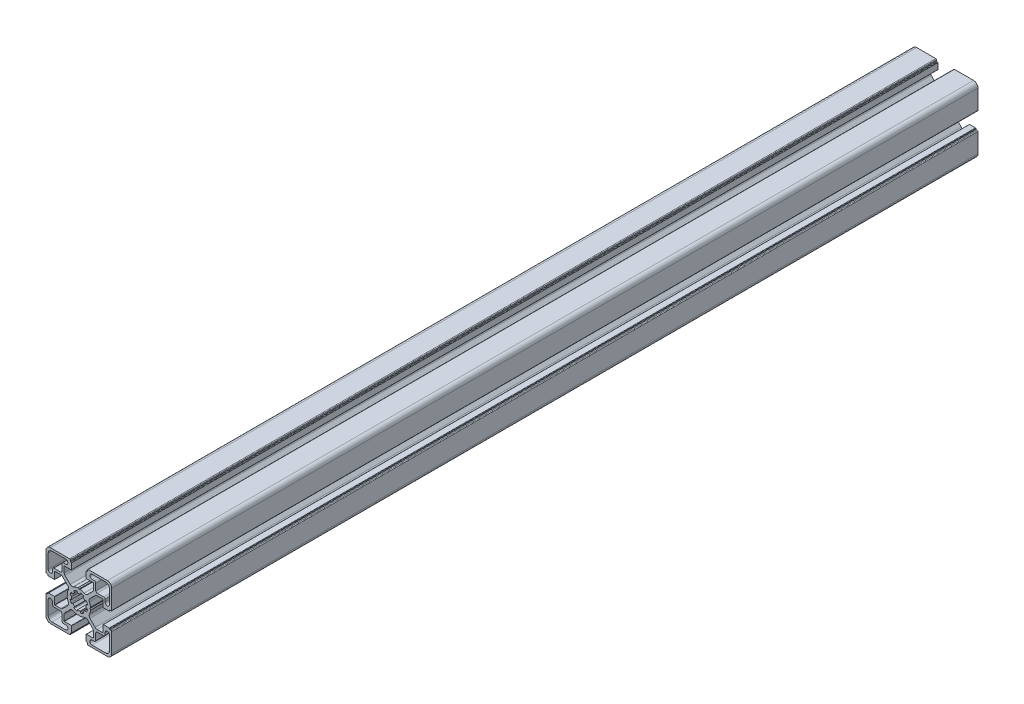
SolidWorks part; units mm, degrees
ref_plane "Front Plane" through (0, 0, 0) normal (0, 0, 1) x (1, 0, 0)
ref_plane "Top Plane" through (0, 0, 0) normal (0, 1, 0) x (1, 0, 0)
ref_plane "Right Plane" through (0, 0, 0) normal (1, 0, 0) x (0, 0, -1)
sketch "Sketch1" plane through (0, 0, 0) normal (0, 0, 1) x (1, 0, 0)
  line L0 (10.55, 18) -> (9, 18)
  line L1 (18.5, 21) -> (9, 21)
  line L2 (21, 9.0002) -> (21, 18.5)
  line L3 (18, 9.0002) -> (18, 10.55)
  line L4 (17, 11.55) -> (12.55, 11.55)
  line L5 (11.55, 12.55) -> (11.55, 17)
  line L6 (7.974, 0.7926) -> (7.5401, 0.0468)
  line L7 (-0.8674, 4.9242) -> (-0.9675, 5.4811)
  line L8 (-3.1913, 4.5626) -> (-2.864, 4.0985)
  line L9 (-4.0897, 2.8765) -> (-4.5668, 3.2082)
  line L10 (-5.4897, 0.9862) -> (-4.9205, 0.8878)
  line L11 (11.1298, 9.425) -> (7.5635, 5.8587)
  line L12 (16.3169, 9.9945) -> (12.5048, 9.9945)
  line L13 (16.5169, 5.2) -> (16.5169, 9.7945)
  line L14 (20.7196, 5) -> (16.7169, 5)
  line L15 (21.0196, 5.3) -> (21.0196, 5.5)
  line L16 (22, 5.8) -> (21.3196, 5.8)
  line L17 (22.5, 6.3) -> (22.5, 19.5)
  line L18 (19.5, 22.5) -> (6.3757, 22.5)
  line L19 (5.8757, 21.3) -> (5.8757, 22)
  line L20 (5.5757, 21) -> (5.3, 21)
  line L21 (5, 16.6668) -> (5, 20.7)
  line L22 (9.9054, 16.4668) -> (5.2, 16.4668)
  line L23 (10.1054, 12.4716) -> (10.1054, 16.2668)
  line L24 (5.9449, 7.4827) -> (9.5196, 11.0574)
  line L25 (0.1126, 7.6069) -> (0.7547, 7.9748)
  line L26 (5.4897, 0.9862) -> (4.9205, 0.8878)
  line L27 (4.0897, 2.8765) -> (4.5668, 3.2082)
  line L28 (3.1913, 4.5626) -> (2.864, 4.0985)
  line L29 (0.8674, 4.9242) -> (0.9675, 5.4811)
  line L30 (-10.55, -18) -> (-9, -18)
  line L31 (-18.5, -21) -> (-9, -21)
  line L32 (-21, -9.0002) -> (-21, -18.5)
  line L33 (-18, -9.0002) -> (-18, -10.55)
  line L34 (-17, -11.55) -> (-12.55, -11.55)
  line L35 (-11.55, -12.55) -> (-11.55, -17)
  line L36 (-7.974, -0.7926) -> (-7.5401, -0.0468)
  line L37 (-11.1298, -9.425) -> (-7.5635, -5.8587)
  line L38 (-16.3169, -9.9945) -> (-12.5048, -9.9945)
  line L39 (-16.5169, -5.2) -> (-16.5169, -9.7945)
  line L40 (-20.7196, -5) -> (-16.7169, -5)
  line L41 (-21.0196, -5.3) -> (-21.0196, -5.5)
  line L42 (-22, -5.8) -> (-21.3196, -5.8)
  line L43 (-22.5, -6.3) -> (-22.5, -19.5)
  line L44 (-19.5, -22.5) -> (-6.3757, -22.5)
  line L45 (-5.8757, -21.3) -> (-5.8757, -22)
  line L46 (-5.5757, -21) -> (-5.3, -21)
  line L47 (-5, -16.6668) -> (-5, -20.7)
  line L48 (-9.9054, -16.4668) -> (-5.2, -16.4668)
  line L49 (-10.1054, -12.4716) -> (-10.1054, -16.2668)
  line L50 (-5.9449, -7.4827) -> (-9.5196, -11.0574)
  line L51 (-0.1126, -7.6069) -> (-0.7547, -7.9748)
  line L52 (0.8674, -4.9242) -> (0.9675, -5.4811)
  line L53 (3.1913, -4.5626) -> (2.864, -4.0985)
  line L54 (4.0897, -2.8765) -> (4.5668, -3.2082)
  line L55 (5.4897, -0.9862) -> (4.9205, -0.8878)
  line L56 (0.1126, -7.6069) -> (0.7547, -7.9748)
  line L57 (5.9449, -7.4827) -> (9.5196, -11.0574)
  line L58 (10.1054, -12.4716) -> (10.1054, -16.2668)
  line L59 (9.9054, -16.4668) -> (5.2, -16.4668)
  line L60 (5, -16.6668) -> (5, -20.7)
  line L61 (5.5757, -21) -> (5.3, -21)
  line L62 (-0.1126, 7.6069) -> (-0.7547, 7.9748)
  line L63 (-5.9449, 7.4827) -> (-9.5196, 11.0574)
  line L64 (-10.1054, 12.4716) -> (-10.1054, 16.2668)
  line L65 (-9.9054, 16.4668) -> (-5.2, 16.4668)
  line L66 (-5, 16.6668) -> (-5, 20.7)
  line L67 (-5.5757, 21) -> (-5.3, 21)
  line L68 (-5.8757, 21.3) -> (-5.8757, 22)
  line L69 (-19.5, 22.5) -> (-6.3757, 22.5)
  line L70 (-22.5, 6.3) -> (-22.5, 19.5)
  line L71 (-22, 5.8) -> (-21.3196, 5.8)
  line L72 (-21.0196, 5.3) -> (-21.0196, 5.5)
  line L73 (-20.7196, 5) -> (-16.7169, 5)
  line L74 (-16.5169, 5.2) -> (-16.5169, 9.7945)
  line L75 (-16.3169, 9.9945) -> (-12.5048, 9.9945)
  line L76 (-11.1298, 9.425) -> (-7.5635, 5.8587)
  line L77 (-7.974, 0.7926) -> (-7.5401, 0.0468)
  line L78 (5.8757, -21.3) -> (5.8757, -22)
  line L79 (19.5, -22.5) -> (6.3757, -22.5)
  line L80 (22.5, -6.3) -> (22.5, -19.5)
  line L81 (22, -5.8) -> (21.3196, -5.8)
  line L82 (21.0196, -5.3) -> (21.0196, -5.5)
  line L83 (20.7196, -5) -> (16.7169, -5)
  line L84 (16.5169, -5.2) -> (16.5169, -9.7945)
  line L85 (16.3169, -9.9945) -> (12.5048, -9.9945)
  line L86 (11.1298, -9.425) -> (7.5635, -5.8587)
  line L87 (-5.4897, -0.9862) -> (-4.9205, -0.8878)
  line L88 (-4.0897, -2.8765) -> (-4.5668, -3.2082)
  line L89 (-3.1913, -4.5626) -> (-2.864, -4.0985)
  line L90 (-0.8674, -4.9242) -> (-0.9675, -5.4811)
  line L91 (7.974, -0.7926) -> (7.5401, -0.0468)
  line L92 (-11.55, 12.55) -> (-11.55, 17)
  line L93 (-17, 11.55) -> (-12.55, 11.55)
  line L94 (-18, 9.0002) -> (-18, 10.55)
  line L95 (-21, 9.0002) -> (-21, 18.5)
  line L96 (-18.5, 21) -> (-9, 21)
  line L97 (-10.55, 18) -> (-9, 18)
  line L98 (11.55, -12.55) -> (11.55, -17)
  line L99 (17, -11.55) -> (12.55, -11.55)
  line L100 (18, -9.0002) -> (18, -10.55)
  line L101 (21, -9.0002) -> (21, -18.5)
  line L102 (18.5, -21) -> (9, -21)
  line L103 (10.55, -18) -> (9, -18)
  line L104 (-33.3633, 0) -> (37.7265, 0) construction
  line L105 (0, 32.2957) -> (0, -36.0465) construction
  arc A0 (9, 18) -> (9, 21) centre (9, 19.5) cw
  arc A1 (18.5, 21) -> (21, 18.5) centre (18.5, 18.5) cw
  arc A2 (21, 9.0002) -> (18, 9.0002) centre (19.5, 9.0002) cw
  arc A3 (17, 11.55) -> (18, 10.55) centre (17, 10.55) cw
  arc A4 (12.55, 11.55) -> (11.55, 12.55) centre (12.55, 12.55) cw
  arc A5 (10.55, 18) -> (11.55, 17) centre (10.55, 17) cw
  arc A6 (7.5313, 0) -> (7.5401, 0.0468) centre (7.7309, -0.013) cw
  arc A7 (8, 0.9141) -> (7.974, 0.7926) centre (7.8011, 0.8932) cw
  arc A8 (7.2004, 3.6119) -> (8, 0.9141) centre (0.0496, 0.0249) cw
  arc A9 (7.2004, 3.6119) -> (7.5635, 5.8587) centre (8.9385, 4.4837) cw
  arc A10 (11.1298, 9.425) -> (12.5048, 9.9945) centre (12.5048, 8.05) cw
  arc A11 (16.3169, 9.9945) -> (16.5169, 9.7945) centre (16.3169, 9.7945) cw
  arc A12 (16.7169, 5) -> (16.5169, 5.2) centre (16.7169, 5.2) cw
  arc A13 (21.0196, 5.3) -> (20.7196, 5) centre (20.7196, 5.3) cw
  arc A14 (0.8674, 4.9242) -> (-0.8674, 4.9242) centre (0, 0) ccw
  arc A15 (-0.9675, 5.4811) -> (-1.5951, 5.8941) centre (-1.4627, 5.4119) ccw
  arc A16 (-1.5951, 5.8941) -> (-3.0444, 5.2994) centre (-0.0235, 0) ccw
  arc A17 (-3.0444, 5.2994) -> (-3.1913, 4.5626) centre (-2.7943, 4.8665) ccw
  arc A18 (-2.864, 4.0985) -> (-4.0897, 2.8765) centre (0, 0) ccw
  arc A19 (-4.5668, 3.2082) -> (-5.3025, 3.0565) centre (-4.868, 2.8091) ccw
  arc A20 (-5.3025, 3.0565) -> (-5.9068, 1.6112) centre (-0.0235, 0) ccw
  arc A21 (-5.9068, 1.6112) -> (-5.4897, 0.9862) centre (-5.4239, 1.4819) ccw
  arc A22 (-4.9205, 0.8878) -> (-5, 0) centre (0, 0) ccw
  arc A23 (21.0196, 5.5) -> (21.3196, 5.8) centre (21.3196, 5.5) cw
  arc A24 (22.5, 6.3) -> (22, 5.8) centre (22, 6.3) cw
  arc A25 (19.5, 22.5) -> (22.5, 19.5) centre (19.5, 19.5) cw
  arc A26 (5.8757, 22) -> (6.3757, 22.5) centre (6.3757, 22) cw
  arc A27 (5.8757, 21.3) -> (5.5757, 21) centre (5.5757, 21.3) cw
  arc A28 (5, 20.7) -> (5.3, 21) centre (5.3, 20.7) cw
  arc A29 (5.2, 16.4668) -> (5, 16.6668) centre (5.2, 16.6668) cw
  arc A30 (9.9054, 16.4668) -> (10.1054, 16.2668) centre (9.9054, 16.2668) cw
  arc A31 (10.1054, 12.4716) -> (9.5196, 11.0574) centre (8.1054, 12.4716) cw
  arc A32 (5.9449, 7.4827) -> (3.6665, 7.1733) centre (4.5855, 8.9496) cw
  arc A33 (0.8764, 8) -> (3.6665, 7.1733) centre (0.0235, 0) cw
  arc A34 (0.7547, 7.9748) -> (0.8764, 8) centre (0.8542, 7.8013) cw
  arc A35 (0.1126, 7.6069) -> (0, 7.531) centre (-0.0489, 7.7249) cw
  arc A36 (4.9205, 0.8878) -> (5, 0) centre (0, 0) cw
  arc A37 (5.9068, 1.6112) -> (5.4897, 0.9862) centre (5.4239, 1.4819) cw
  arc A38 (5.3025, 3.0565) -> (5.9068, 1.6112) centre (0.0235, 0) cw
  arc A39 (4.5668, 3.2082) -> (5.3025, 3.0565) centre (4.868, 2.8091) cw
  arc A40 (2.864, 4.0985) -> (4.0897, 2.8765) centre (0, 0) cw
  arc A41 (3.0444, 5.2994) -> (3.1913, 4.5626) centre (2.7943, 4.8665) cw
  arc A42 (1.5951, 5.8941) -> (3.0444, 5.2994) centre (0.0235, 0) cw
  arc A43 (0.9675, 5.4811) -> (1.5951, 5.8941) centre (1.4627, 5.4119) cw
  arc A44 (-9, -18) -> (-9, -21) centre (-9, -19.5) cw
  arc A45 (-18.5, -21) -> (-21, -18.5) centre (-18.5, -18.5) cw
  arc A46 (-21, -9.0002) -> (-18, -9.0002) centre (-19.5, -9.0002) cw
  arc A47 (-17, -11.55) -> (-18, -10.55) centre (-17, -10.55) cw
  arc A48 (-12.55, -11.55) -> (-11.55, -12.55) centre (-12.55, -12.55) cw
  arc A49 (-10.55, -18) -> (-11.55, -17) centre (-10.55, -17) cw
  arc A50 (-7.5313, 0) -> (-7.5401, -0.0468) centre (-7.7309, 0.013) cw
  arc A51 (-8, -0.9141) -> (-7.974, -0.7926) centre (-7.8011, -0.8932) cw
  arc A52 (-7.2004, -3.6119) -> (-8, -0.9141) centre (-0.0496, -0.0249) cw
  arc A53 (-7.2004, -3.6119) -> (-7.5635, -5.8587) centre (-8.9385, -4.4837) cw
  arc A54 (-11.1298, -9.425) -> (-12.5048, -9.9945) centre (-12.5048, -8.05) cw
  arc A55 (-16.3169, -9.9945) -> (-16.5169, -9.7945) centre (-16.3169, -9.7945) cw
  arc A56 (-16.7169, -5) -> (-16.5169, -5.2) centre (-16.7169, -5.2) cw
  arc A57 (-21.0196, -5.3) -> (-20.7196, -5) centre (-20.7196, -5.3) cw
  arc A58 (-21.0196, -5.5) -> (-21.3196, -5.8) centre (-21.3196, -5.5) cw
  arc A59 (-22.5, -6.3) -> (-22, -5.8) centre (-22, -6.3) cw
  arc A60 (-19.5, -22.5) -> (-22.5, -19.5) centre (-19.5, -19.5) cw
  arc A61 (-5.8757, -22) -> (-6.3757, -22.5) centre (-6.3757, -22) cw
  arc A62 (-5.8757, -21.3) -> (-5.5757, -21) centre (-5.5757, -21.3) cw
  arc A63 (-5, -20.7) -> (-5.3, -21) centre (-5.3, -20.7) cw
  arc A64 (-5.2, -16.4668) -> (-5, -16.6668) centre (-5.2, -16.6668) cw
  arc A65 (-9.9054, -16.4668) -> (-10.1054, -16.2668) centre (-9.9054, -16.2668) cw
  arc A66 (-10.1054, -12.4716) -> (-9.5196, -11.0574) centre (-8.1054, -12.4716) cw
  arc A67 (-5.9449, -7.4827) -> (-3.6665, -7.1733) centre (-4.5855, -8.9496) cw
  arc A68 (-0.8764, -8) -> (-3.6665, -7.1733) centre (-0.0235, 0) cw
  arc A69 (-0.7547, -7.9748) -> (-0.8764, -8) centre (-0.8542, -7.8013) cw
  arc A70 (-0.1126, -7.6069) -> (0, -7.531) centre (0.0489, -7.7249) cw
  arc A71 (0.9675, -5.4811) -> (1.5951, -5.8941) centre (1.4627, -5.4119) ccw
  arc A72 (1.5951, -5.8941) -> (3.0444, -5.2994) centre (0.0235, 0) ccw
  arc A73 (3.0444, -5.2994) -> (3.1913, -4.5626) centre (2.7943, -4.8665) ccw
  arc A74 (2.864, -4.0985) -> (4.0897, -2.8765) centre (0, 0) ccw
  arc A75 (4.5668, -3.2082) -> (5.3025, -3.0565) centre (4.868, -2.8091) ccw
  arc A76 (5.3025, -3.0565) -> (5.9068, -1.6112) centre (0.0235, 0) ccw
  arc A77 (5.9068, -1.6112) -> (5.4897, -0.9862) centre (5.4239, -1.4819) ccw
  arc A78 (4.9205, -0.8878) -> (5, 0) centre (0, 0) ccw
  arc A79 (0.1126, -7.6069) -> (0, -7.531) centre (-0.0489, -7.7249) ccw
  arc A80 (0.7547, -7.9748) -> (0.8764, -8) centre (0.8542, -7.8013) ccw
  arc A81 (0.8764, -8) -> (3.6665, -7.1733) centre (0.0235, 0) ccw
  arc A82 (5.9449, -7.4827) -> (3.6665, -7.1733) centre (4.5855, -8.9496) ccw
  arc A83 (10.1054, -12.4716) -> (9.5196, -11.0574) centre (8.1054, -12.4716) ccw
  arc A84 (9.9054, -16.4668) -> (10.1054, -16.2668) centre (9.9054, -16.2668) ccw
  arc A85 (5.2, -16.4668) -> (5, -16.6668) centre (5.2, -16.6668) ccw
  arc A86 (5, -20.7) -> (5.3, -21) centre (5.3, -20.7) ccw
  arc A87 (5.8757, -21.3) -> (5.5757, -21) centre (5.5757, -21.3) ccw
  arc A88 (-0.1126, 7.6069) -> (0, 7.531) centre (0.0489, 7.7249) ccw
  arc A89 (-0.7547, 7.9748) -> (-0.8764, 8) centre (-0.8542, 7.8013) ccw
  arc A90 (-0.8764, 8) -> (-3.6665, 7.1733) centre (-0.0235, 0) ccw
  arc A91 (-5.9449, 7.4827) -> (-3.6665, 7.1733) centre (-4.5855, 8.9496) ccw
  arc A92 (-10.1054, 12.4716) -> (-9.5196, 11.0574) centre (-8.1054, 12.4716) ccw
  arc A93 (-9.9054, 16.4668) -> (-10.1054, 16.2668) centre (-9.9054, 16.2668) ccw
  arc A94 (-5.2, 16.4668) -> (-5, 16.6668) centre (-5.2, 16.6668) ccw
  arc A95 (-5, 20.7) -> (-5.3, 21) centre (-5.3, 20.7) ccw
  arc A96 (-5.8757, 21.3) -> (-5.5757, 21) centre (-5.5757, 21.3) ccw
  arc A97 (-5.8757, 22) -> (-6.3757, 22.5) centre (-6.3757, 22) ccw
  arc A98 (-19.5, 22.5) -> (-22.5, 19.5) centre (-19.5, 19.5) ccw
  arc A99 (-22.5, 6.3) -> (-22, 5.8) centre (-22, 6.3) ccw
  arc A100 (-21.0196, 5.5) -> (-21.3196, 5.8) centre (-21.3196, 5.5) ccw
  arc A101 (-21.0196, 5.3) -> (-20.7196, 5) centre (-20.7196, 5.3) ccw
  arc A102 (-16.7169, 5) -> (-16.5169, 5.2) centre (-16.7169, 5.2) ccw
  arc A103 (-16.3169, 9.9945) -> (-16.5169, 9.7945) centre (-16.3169, 9.7945) ccw
  arc A104 (-11.1298, 9.425) -> (-12.5048, 9.9945) centre (-12.5048, 8.05) ccw
  arc A105 (-7.2004, 3.6119) -> (-7.5635, 5.8587) centre (-8.9385, 4.4837) ccw
  arc A106 (-7.2004, 3.6119) -> (-8, 0.9141) centre (-0.0496, 0.0249) ccw
  arc A107 (-8, 0.9141) -> (-7.974, 0.7926) centre (-7.8011, 0.8932) ccw
  arc A108 (-7.5313, 0) -> (-7.5401, 0.0468) centre (-7.7309, -0.013) ccw
  arc A109 (5.8757, -22) -> (6.3757, -22.5) centre (6.3757, -22) ccw
  arc A110 (19.5, -22.5) -> (22.5, -19.5) centre (19.5, -19.5) ccw
  arc A111 (22.5, -6.3) -> (22, -5.8) centre (22, -6.3) ccw
  arc A112 (21.0196, -5.5) -> (21.3196, -5.8) centre (21.3196, -5.5) ccw
  arc A113 (-4.9205, -0.8878) -> (-5, 0) centre (0, 0) cw
  arc A114 (-5.9068, -1.6112) -> (-5.4897, -0.9862) centre (-5.4239, -1.4819) cw
  arc A115 (-5.3025, -3.0565) -> (-5.9068, -1.6112) centre (-0.0235, 0) cw
  arc A116 (-4.5668, -3.2082) -> (-5.3025, -3.0565) centre (-4.868, -2.8091) cw
  arc A117 (-2.864, -4.0985) -> (-4.0897, -2.8765) centre (0, 0) cw
  arc A118 (-3.0444, -5.2994) -> (-3.1913, -4.5626) centre (-2.7943, -4.8665) cw
  arc A119 (-1.5951, -5.8941) -> (-3.0444, -5.2994) centre (-0.0235, 0) cw
  arc A120 (-0.9675, -5.4811) -> (-1.5951, -5.8941) centre (-1.4627, -5.4119) cw
  arc A121 (0.8674, -4.9242) -> (-0.8674, -4.9242) centre (0, 0) cw
  arc A122 (21.0196, -5.3) -> (20.7196, -5) centre (20.7196, -5.3) ccw
  arc A123 (16.7169, -5) -> (16.5169, -5.2) centre (16.7169, -5.2) ccw
  arc A124 (-10.55, 18) -> (-11.55, 17) centre (-10.55, 17) ccw
  arc A125 (-12.55, 11.55) -> (-11.55, 12.55) centre (-12.55, 12.55) ccw
  arc A126 (-17, 11.55) -> (-18, 10.55) centre (-17, 10.55) ccw
  arc A127 (-21, 9.0002) -> (-18, 9.0002) centre (-19.5, 9.0002) ccw
  arc A128 (-18.5, 21) -> (-21, 18.5) centre (-18.5, 18.5) ccw
  arc A129 (-9, 18) -> (-9, 21) centre (-9, 19.5) ccw
  arc A130 (16.3169, -9.9945) -> (16.5169, -9.7945) centre (16.3169, -9.7945) ccw
  arc A131 (11.1298, -9.425) -> (12.5048, -9.9945) centre (12.5048, -8.05) ccw
  arc A132 (7.2004, -3.6119) -> (7.5635, -5.8587) centre (8.9385, -4.4837) ccw
  arc A133 (7.2004, -3.6119) -> (8, -0.9141) centre (0.0496, -0.0249) ccw
  arc A134 (8, -0.9141) -> (7.974, -0.7926) centre (7.8011, -0.8932) ccw
  arc A135 (7.5313, 0) -> (7.5401, -0.0468) centre (7.7309, 0.013) ccw
  arc A136 (10.55, -18) -> (11.55, -17) centre (10.55, -17) ccw
  arc A137 (12.55, -11.55) -> (11.55, -12.55) centre (12.55, -12.55) ccw
  arc A138 (17, -11.55) -> (18, -10.55) centre (17, -10.55) ccw
  arc A139 (21, -9.0002) -> (18, -9.0002) centre (19.5, -9.0002) ccw
  arc A140 (18.5, -21) -> (21, -18.5) centre (18.5, -18.5) ccw
  arc A141 (9, -18) -> (9, -21) centre (9, -19.5) ccw
  dimension "D6" = 12.2
  dimension "D8" = 10
  dimension "D1" = 10
  dimension "D2" = 45
  dimension "D3" = 45
  dimension "D4" = 10
  dimension "D5" = 14.5
  dimension "D7" = 22.5
extrude "Base-Extrude" add sketch "Sketch1" against normal blind 593
